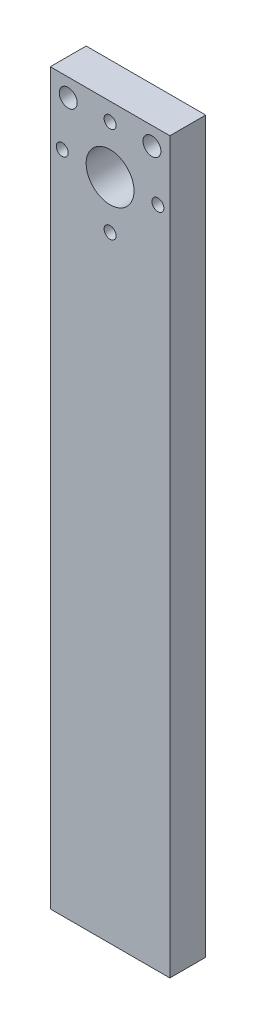
SolidWorks part; units mm, degrees
ref_plane "Plan de face" through (0, 0, 0) normal (0, 0, 1) x (1, 0, 0)
ref_plane "Plan de dessus" through (0, 0, 0) normal (0, 1, 0) x (1, 0, 0)
ref_plane "Plan de droite" through (0, 0, 0) normal (1, 0, 0) x (0, 0, -1)
sketch "Esquisse1" plane through (0, 0, 0) normal (0, 0, 1) x (1, 0, 0)
  line L1 (-10, 84) -> (10, 84)
  line L2 (-10, 84) -> (-10, -38)
  line L3 (-10, -38) -> (10, -38)
  line L4 (10, 84) -> (10, -38)
  dimension "D1" = 122
  dimension "D2" = 20
  dimension "D3" = 10
  dimension "D4" = 38
extrude "Boss.-Extru.1" add sketch "Esquisse1" along normal blind 6
sketch "Esquisse2" plane through (0, 0, 6) normal (0, 0, 1) x (1, 0, 0)
  line L0 (10, 84) -> (-10, 84) construction
  line L1 (45.7904, 0) -> (-37.4617, 0) construction
  line L2 (-19.8072, 81) -> (29.1642, 81) construction
  line L3 (-10, 84) -> (-10, -38) construction
  line L4 (10, -38) -> (10, 84) construction
  circle A0 centre (0, 73) radius 4
  circle A1 centre (0, 73) radius 8 construction
  circle A2 centre (0, 81) radius 1
  circle A3 centre (-8, 73) radius 1
  circle A4 centre (0, 65) radius 1
  circle A5 centre (8, 73) radius 1
  circle A6 centre (-7, 81) radius 1.5
  circle A7 centre (7, 81) radius 1.5
  dimension "D1" = 8
  dimension "D2" = 16
  dimension "D3" = 2
  dimension "D4" = 2
  dimension "D5" = 2
  dimension "D6" = 2
  dimension "D9" = 3
  dimension "D10" = 3
  dimension "D11" = 3
  dimension "D12" = 3
  dimension "D7" = 11
  dimension "D8" = 3
extrude "Enlèv. mat.-Extru.1" cut sketch "Esquisse2" against normal blind 6
equation "\"D3@Esquisse1\"=\"D2@Esquisse1\"/2"
equation "\"D4@Esquisse1\"=\"D1@Esquisse1\"/2"
